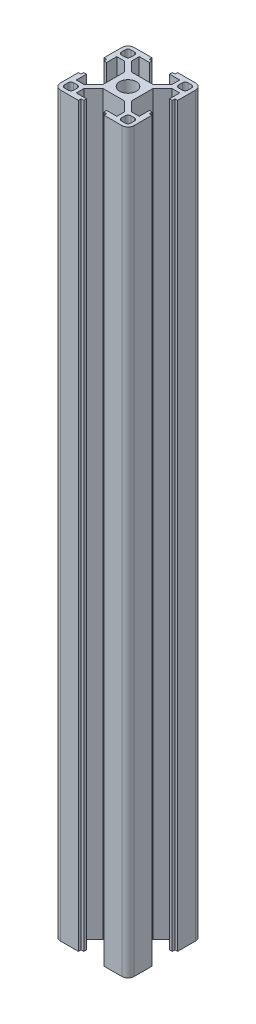
SolidWorks part; units mm, degrees
ref_plane "Front Plane" through (0, 0, 0) normal (0, 0, 1) x (1, 0, 0)
ref_plane "Top Plane" through (0, 0, 0) normal (0, 1, 0) x (1, 0, 0)
ref_plane "Right Plane" through (0, 0, 0) normal (1, 0, 0) x (0, 0, -1)
ref_plane "Plane1" through (0, 100, 0) normal (0, 1, 0) x (1, 0, 0)
sketch "Sketch1" plane through (0, 100, 0) normal (0, 1, 0) x (1, 0, 0)
  line L0 (28.5, -25.9) -> (28.5, -27.35)
  line L1 (27.35, -28.5) -> (25.9, -28.5)
  line L2 (24.75, -27.35) -> (24.75, -25.9)
  line L3 (25.9, -24.75) -> (27.35, -24.75)
  line L4 (1.5, -27.35) -> (1.5, -25.9)
  line L5 (2.65, -24.75) -> (4.1, -24.75)
  line L6 (5.25, -25.9) -> (5.25, -27.35)
  line L7 (4.1, -28.5) -> (2.65, -28.5)
  line L8 (2.65, -1.5) -> (4.1, -1.5)
  line L9 (5.25, -2.65) -> (5.25, -4.1)
  line L10 (4.1, -5.25) -> (2.65, -5.25)
  line L11 (1.5, -4.1) -> (1.5, -2.65)
  line L12 (28.5, -2.65) -> (28.5, -4.1)
  line L13 (27.35, -5.25) -> (25.9, -5.25)
  line L14 (24.75, -4.1) -> (24.75, -2.65)
  line L15 (25.9, -1.5) -> (27.35, -1.5)
  line L16 (27.5, 0) -> (20.2, 0)
  line L17 (20.2, 0) -> (20.2, -1.1)
  line L18 (20.2, -1.1) -> (19.1, -1.1)
  line L19 (19.1, -1.1) -> (19.1, -2.2)
  line L20 (19.1, -2.2) -> (23.25, -2.2)
  line L21 (23.25, -2.2) -> (23.25, -5.3358)
  line L22 (23.25, -5.3358) -> (19.3858, -9.2)
  line L23 (19.3858, -9.2) -> (10.6142, -9.2)
  line L24 (10.6142, -9.2) -> (6.75, -5.3358)
  line L25 (6.75, -5.3358) -> (6.75, -2.2)
  line L26 (6.75, -2.2) -> (10.9, -2.2)
  line L27 (10.9, -2.2) -> (10.9, -1.1)
  line L28 (10.9, -1.1) -> (9.8, -1.1)
  line L29 (9.8, -1.1) -> (9.8, 0)
  line L30 (9.8, 0) -> (2.5, 0)
  line L31 (0, -2.5) -> (0, -9.8)
  line L32 (0, -9.8) -> (1.1, -9.8)
  line L33 (1.1, -9.8) -> (1.1, -10.9)
  line L34 (1.1, -10.9) -> (2.2, -10.9)
  line L35 (2.2, -10.9) -> (2.2, -6.75)
  line L36 (2.2, -6.75) -> (5.3358, -6.75)
  line L37 (5.3358, -6.75) -> (9.2, -10.6142)
  line L38 (9.2, -10.6142) -> (9.2, -19.3858)
  line L39 (9.2, -19.3858) -> (5.3358, -23.25)
  line L40 (5.3358, -23.25) -> (2.2, -23.25)
  line L41 (2.2, -23.25) -> (2.2, -19.1)
  line L42 (2.2, -19.1) -> (1.1, -19.1)
  line L43 (1.1, -19.1) -> (1.1, -20.2)
  line L44 (1.1, -20.2) -> (0, -20.2)
  line L45 (0, -20.2) -> (0, -27.5)
  line L46 (2.5, -30) -> (9.8, -30)
  line L47 (9.8, -30) -> (9.8, -28.9)
  line L48 (9.8, -28.9) -> (10.9, -28.9)
  line L49 (10.9, -28.9) -> (10.9, -27.8)
  line L50 (10.9, -27.8) -> (6.75, -27.8)
  line L51 (6.75, -27.8) -> (6.75, -24.6642)
  line L52 (6.75, -24.6642) -> (10.6142, -20.8)
  line L53 (10.6142, -20.8) -> (19.3858, -20.8)
  line L54 (19.3858, -20.8) -> (23.25, -24.6642)
  line L55 (23.25, -24.6642) -> (23.25, -27.8)
  line L56 (23.25, -27.8) -> (19.1, -27.8)
  line L57 (19.1, -27.8) -> (19.1, -28.9)
  line L58 (19.1, -28.9) -> (20.2, -28.9)
  line L59 (20.2, -28.9) -> (20.2, -30)
  line L60 (20.2, -30) -> (27.5, -30)
  line L61 (30, -27.5) -> (30, -20.2)
  line L62 (30, -20.2) -> (28.9, -20.2)
  line L63 (28.9, -20.2) -> (28.9, -19.1)
  line L64 (28.9, -19.1) -> (27.8, -19.1)
  line L65 (27.8, -19.1) -> (27.8, -23.25)
  line L66 (27.8, -23.25) -> (24.6642, -23.25)
  line L67 (24.6642, -23.25) -> (20.8, -19.3858)
  line L68 (20.8, -19.3858) -> (20.8, -10.6142)
  line L69 (20.8, -10.6142) -> (24.6642, -6.75)
  line L70 (24.6642, -6.75) -> (27.8, -6.75)
  line L71 (27.8, -6.75) -> (27.8, -10.9)
  line L72 (27.8, -10.9) -> (28.9, -10.9)
  line L73 (28.9, -10.9) -> (28.9, -9.8)
  line L74 (28.9, -9.8) -> (30, -9.8)
  line L75 (30, -9.8) -> (30, -2.5)
  arc A0 (27.35, -24.75) -> (28.5, -25.9) centre (27.35, -25.9) cw
  arc A1 (28.5, -27.35) -> (27.35, -28.5) centre (27.35, -27.35) cw
  arc A2 (25.9, -28.5) -> (24.75, -27.35) centre (25.9, -27.35) cw
  arc A3 (24.75, -25.9) -> (25.9, -24.75) centre (25.9, -25.9) cw
  arc A4 (2.65, -28.5) -> (1.5, -27.35) centre (2.65, -27.35) cw
  arc A5 (1.5, -25.9) -> (2.65, -24.75) centre (2.65, -25.9) cw
  arc A6 (4.1, -24.75) -> (5.25, -25.9) centre (4.1, -25.9) cw
  arc A7 (5.25, -27.35) -> (4.1, -28.5) centre (4.1, -27.35) cw
  arc A8 (1.5, -2.65) -> (2.65, -1.5) centre (2.65, -2.65) cw
  arc A9 (4.1, -1.5) -> (5.25, -2.65) centre (4.1, -2.65) cw
  arc A10 (5.25, -4.1) -> (4.1, -5.25) centre (4.1, -4.1) cw
  arc A11 (2.65, -5.25) -> (1.5, -4.1) centre (2.65, -4.1) cw
  arc A12 (27.35, -1.5) -> (28.5, -2.65) centre (27.35, -2.65) cw
  arc A13 (28.5, -4.1) -> (27.35, -5.25) centre (27.35, -4.1) cw
  arc A14 (25.9, -5.25) -> (24.75, -4.1) centre (25.9, -4.1) cw
  arc A15 (24.75, -2.65) -> (25.9, -1.5) centre (25.9, -2.65) cw
  circle A16 centre (15, -15) radius 3.4
  arc A17 (30, -2.5) -> (27.5, 0) centre (27.5, -2.5) ccw
  arc A18 (2.5, 0) -> (0, -2.5) centre (2.5, -2.5) ccw
  arc A19 (0, -27.5) -> (2.5, -30) centre (2.5, -27.5) ccw
  arc A20 (27.5, -30) -> (30, -27.5) centre (27.5, -27.5) ccw
extrude "Boss-Extrude1" add sketch "Sketch1" against normal blind 300
